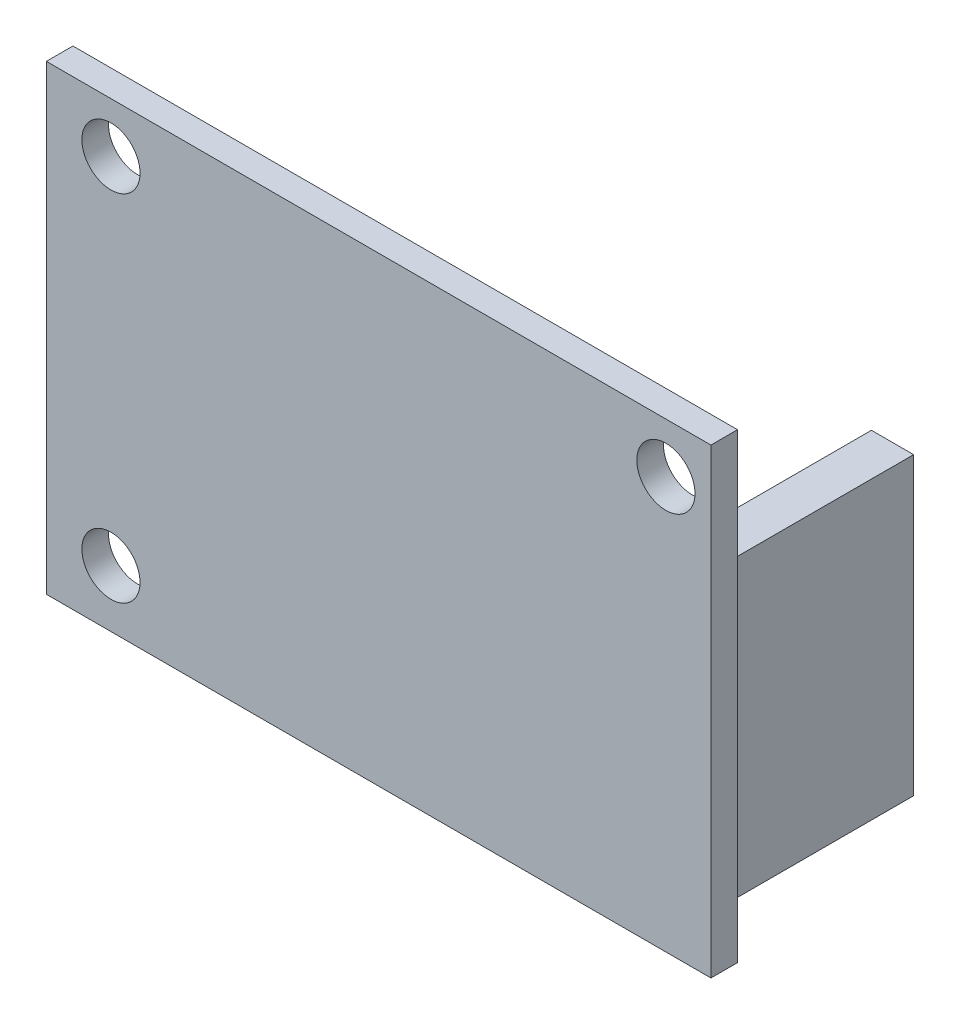
SolidWorks part; units mm, degrees
ref_plane "前视基准面" through (0, 0, 0) normal (0, 0, 1) x (1, 0, 0)
ref_plane "上视基准面" through (0, 0, 0) normal (0, 1, 0) x (1, 0, 0)
ref_plane "右视基准面" through (0, 0, 0) normal (1, 0, 0) x (0, 0, -1)
sketch "草图1" plane through (0, 0, 0) normal (0, 0, 1) x (1, 0, 0)
  line L1 (-10.668, 55.3721) -> (-8.128, 55.3721)
  line L2 (-10.668, 55.3721) -> (-10.668, 37.5921)
  line L3 (-10.668, 37.5921) -> (-8.128, 37.5921)
  line L4 (-8.128, 55.3721) -> (-8.128, 37.5921)
  point P4 (-10.5948, 55.2514)
  point P5 (0, 0)
  dimension "D1" = 2.54
  dimension "D2" = 17.78
extrude "凸台-拉伸1" add sketch "草图1" along normal blind 11
sketch "草图2" plane through (0, 0, 11) normal (0, 0, 1) x (1, 0, 0)
  line L0 (-8.128, 37.5921) -> (-8.128, 55.3721) construction
  line L1 (-7.728, 62.3721) -> (-47.728, 62.3721)
  line L2 (-7.728, 62.3721) -> (-7.728, 34.5921)
  line L3 (-7.728, 34.5921) -> (-47.728, 34.5921)
  line L4 (-47.728, 62.3721) -> (-47.728, 34.5921)
  line L5 (-10.668, 37.5921) -> (-8.128, 37.5921) construction
  line L6 (-8.128, 55.3721) -> (-10.668, 55.3721) construction
  circle A0 centre (-10.4394, 59.3599) radius 1.75
  circle A1 centre (-43.8405, 59.3599) radius 1.75
  circle A2 centre (-43.8405, 38.0239) radius 1.75
  point P13 (0, 0)
  point P17 (0, 0)
  dimension "D5" = 3.5
  dimension "D6" = 3.5
  dimension "D7" = 3.5
  dimension "D1" = 0.4
  dimension "D2" = 3
  dimension "D3" = 7
  dimension "D4" = 40
extrude "凸台-拉伸2" add sketch "草图2" along normal blind 1.6
